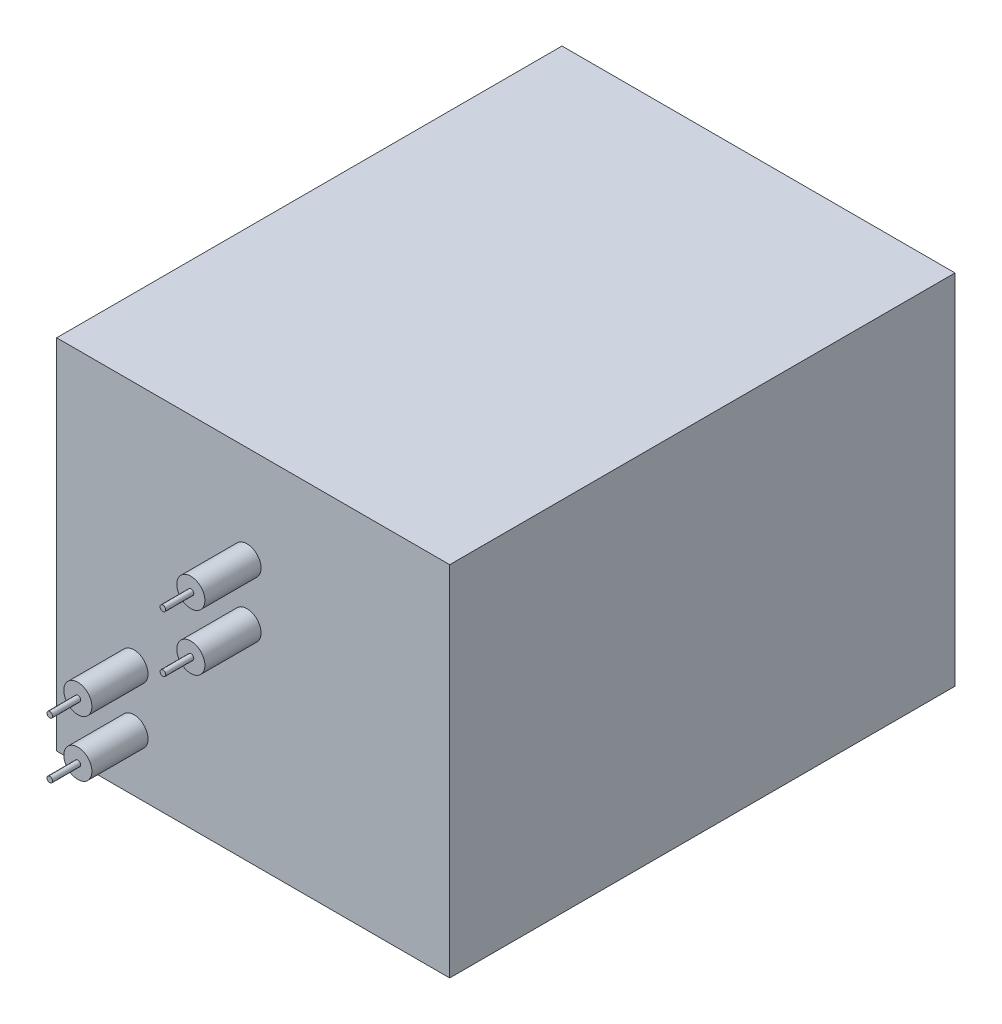
SolidWorks part; units mm, degrees
ref_plane "Front Plane" through (0, 0, 0) normal (0, 0, 1) x (1, 0, 0)
ref_plane "Top Plane" through (0, 0, 0) normal (0, 1, 0) x (1, 0, 0)
ref_plane "Right Plane" through (0, 0, 0) normal (1, 0, 0) x (0, 0, -1)
sketch "Sketch1" plane through (0, 0, 0) normal (0, 1, 0) x (1, 0, 0)
  line L1 (-88.9, -114.3) -> (88.9, -114.3)
  line L2 (-88.9, -114.3) -> (-88.9, 114.3)
  line L3 (-88.9, 114.3) -> (88.9, 114.3)
  line L4 (88.9, -114.3) -> (88.9, 114.3)
  line L5 (-88.9, -114.3) -> (88.9, 114.3) construction
  line L6 (-88.9, 114.3) -> (88.9, -114.3) construction
  point P0 (0, 0)
  dimension "D1" = 177.8
  dimension "D2" = 228.6
extrude "Boss-Extrude1" add sketch "Sketch1" along normal blind 161.925
sketch "Sketch2" plane through (0, 0, 114.3) normal (0, 0, 1) x (1, 0, 0)
  circle A0 centre (-2.7923, 117.9073) radius 6.35
  dimension "D1" = 12.7
extrude "Boss-Extrude2" add sketch "Sketch2" along normal blind 25.4
sketch "Sketch4" plane through (0, 0, 114.3) normal (0, 0, 1) x (1, 0, 0)
  line L0 (-88.9, 0) -> (88.9, 0) construction
  circle A0 centre (-53.9136, 25.4) radius 6.35
  dimension "D1" = 12.7
  dimension "D2" = 25.4
extrude "Boss-Extrude4" add sketch "Sketch4" along normal blind 25.4
pattern_linear "LPattern1" count 2 spacing 25.4 along (0, -1, 0) of "Boss-Extrude2"
pattern_linear "LPattern2" count 2 spacing 25.4 along (0, 1, 0) of "Boss-Extrude4"
sketch "Sketch5" plane through (0, 0, 139.7) normal (0, 0, 1) x (1, 0, 0)
  circle A0 centre (-2.7305, 118.0797) radius 1.27
  dimension "D1" = 2.54
extrude "Boss-Extrude5" add sketch "Sketch5" along normal blind 12.7
pattern_linear "LPattern3" count 2 spacing 25.4 along (0, -1, 0) of "Boss-Extrude5"
sketch "Sketch6" plane through (0, 0, 139.7) normal (0, 0, 1) x (1, 0, 0)
  circle A0 centre (-53.9136, 50.8) radius 1.27
  dimension "D1" = 2.54
extrude "Boss-Extrude6" add sketch "Sketch6" along normal blind 12.7
pattern_linear "LPattern4" count 2 spacing 25.4 along (0, -1, 0) of "Boss-Extrude6"
